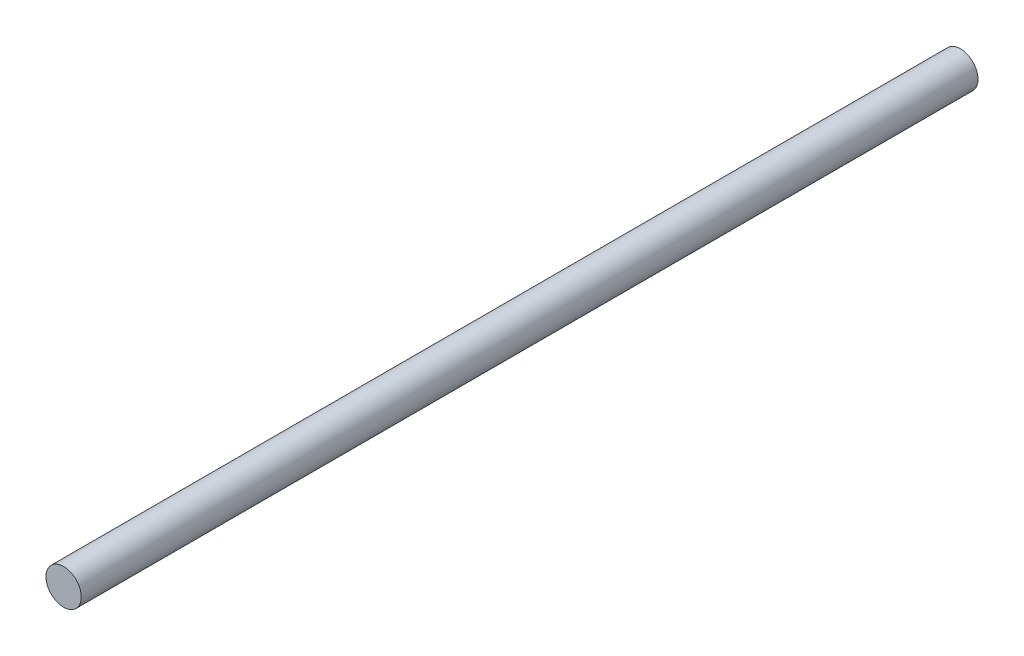
SolidWorks part; units mm, degrees
ref_plane "Front Plane" through (0, 0, 0) normal (0, 0, 1) x (1, 0, 0)
ref_plane "Top Plane" through (0, 0, 0) normal (0, 1, 0) x (1, 0, 0)
ref_plane "Right Plane" through (0, 0, 0) normal (1, 0, 0) x (0, 0, -1)
sketch "Sketch1" plane through (0, 0, 0) normal (0, 0, 1) x (1, 0, 0)
  circle A0 centre (-0.9145, 1.2736) radius 2.5
  dimension "D1" = 5
extrude "Boss-Extrude1" add sketch "Sketch1" along normal blind 127
